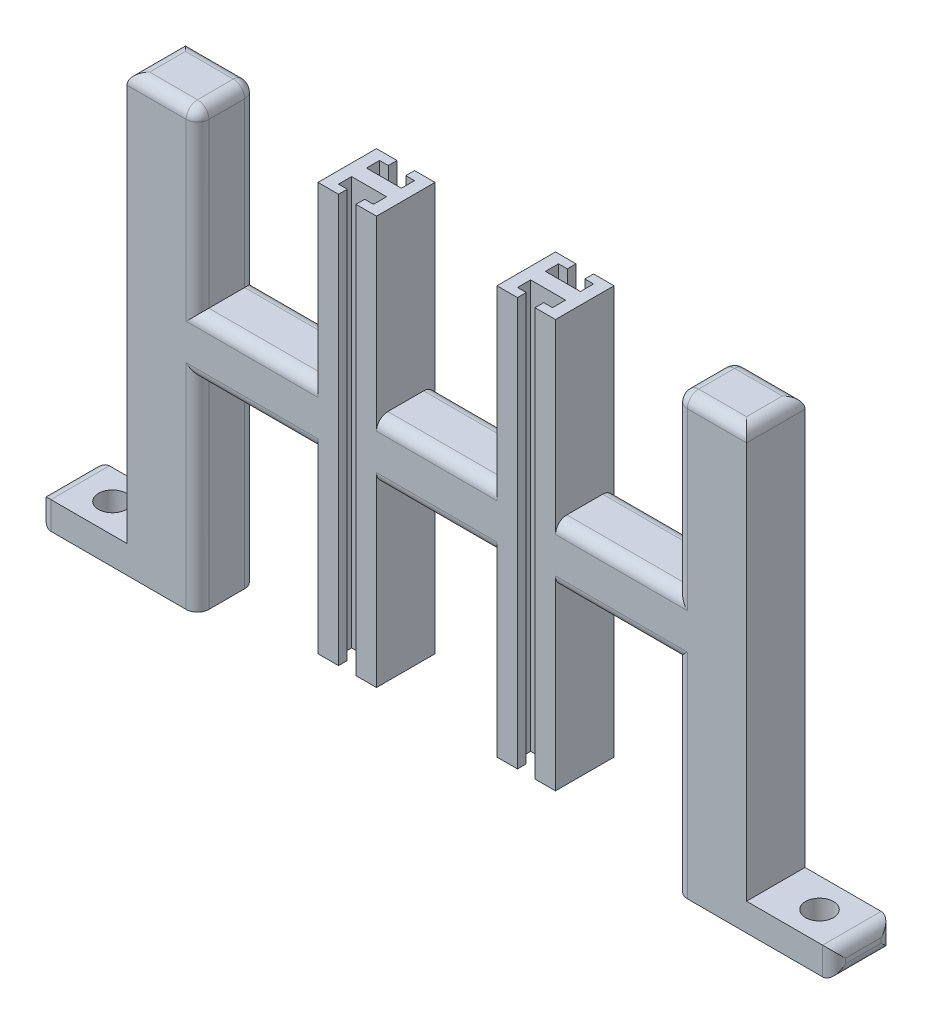
SolidWorks part; units mm, degrees
ref_plane "Front Plane" through (0, 0, 0) normal (0, 0, 1) x (1, 0, 0)
ref_plane "Top Plane" through (0, 0, 0) normal (0, 1, 0) x (1, 0, 0)
ref_plane "Right Plane" through (0, 0, 0) normal (1, 0, 0) x (0, 0, -1)
sketch "Sketch1" plane through (0, 0, 0) normal (0, 0, 1) x (1, 0, 0)
  line L1 (-45, -4.25) -> (45, -4.25)
  line L2 (-45, -4.25) -> (-45, 4.25)
  line L3 (-45, 4.25) -> (45, 4.25)
  line L4 (45, -4.25) -> (45, 4.25)
  line L5 (-45, -4.25) -> (45, 4.25) construction
  line L6 (-45, 4.25) -> (45, -4.25) construction
  point P0 (0, 0)
  dimension "D1" = 8.5
  dimension "D2" = 90
extrude "Boss-Extrude1" add sketch "Sketch1" along normal blind 8.5
sketch "Sketch2" plane through (0, 4.25, 0) normal (0, 1, 0) x (1, 0, 0)
  line L0 (45, -8.5) -> (45, 0) construction
  line L2 (8.75, -8.5) -> (8.75, 0)
  line L4 (0, -13.4309) -> (0, 4.4751) construction
  line L5 (45, 0) -> (-45, 0) construction
  line L6 (-8.75, 0) -> (-17.25, 0)
  line L7 (-17.25, 0) -> (-17.25, -8.5)
  line L8 (45, -8.5) -> (-45, -8.5) construction
  line L9 (-17.25, -8.5) -> (-8.75, -8.5)
  line L10 (-8.75, -8.5) -> (-8.75, 0)
  line L11 (8.75, 0) -> (17.25, 0)
  line L12 (17.25, 0) -> (17.25, -8.5)
  line L13 (17.25, -8.5) -> (8.75, -8.5)
  point P4 (45, -4.25)
  point P16 (-8.75, -4.25)
  point P19 (0, -4.4779)
  dimension "D1" = 17.5
  dimension "D2" = 8.75
  dimension "D3" = 8.5
  dimension "D4" = 8.5
extrude "Boss-Extrude2" add sketch "Sketch2" along normal blind 25.4 and the other way blind 33.9
sketch "Sketch3" plane through (0, 4.25, 0) normal (0, 1, 0) x (1, 0, 0)
  line L0 (-34.75, 0) -> (-34.75, -8.5)
  line L1 (-17.25, 0) -> (-45, 0) construction
  line L3 (-45, -8.5) -> (-45, 0) construction
  line L4 (-17.25, -8.5) -> (-45, -8.5) construction
  line L5 (-45, 0) -> (-34.75, 0)
  line L6 (34.75, 0) -> (34.75, -8.5)
  line L7 (45, 0) -> (17.25, 0) construction
  line L8 (45, -8.5) -> (17.25, -8.5) construction
  line L9 (34.75, -8.5) -> (45, -8.5)
  line L10 (45, 0) -> (45, -8.5)
  line L11 (45, 0) -> (34.75, 0)
  line L12 (-17.25, -8.5) -> (-17.25, 0) construction
  line L13 (17.25, 0) -> (17.25, -8.5) construction
  line L14 (-45, -8.5) -> (-34.75, -8.5)
  line L15 (-45, 0) -> (-45, -8.5)
  dimension "D1" = 17.5
  dimension "D2" = 17.5
extrude "Boss-Extrude3" add sketch "Sketch3" along normal blind 25.4 and the other way blind 37.9
sketch "Sketch4" plane through (45, 0, 0) normal (1, 0, 0) x (0, 0, -1)
  line L0 (-8.5, -33.65) -> (0, -33.65)
  line L1 (0, -33.65) -> (0, -29.65)
  line L2 (0, -33.65) -> (0, 29.65) construction
  line L3 (0, -29.65) -> (-8.5, -29.65)
  line L4 (-8.5, -33.65) -> (-8.5, 29.65) construction
  line L5 (-8.5, -29.65) -> (-8.5, -33.65)
  dimension "D1" = 4
extrude "Boss-Extrude4" add sketch "Sketch4" along normal blind 12.7
sketch "Sketch5" plane through (-45, 0, 0) normal (-1, 0, 0) x (0, 0, 1)
  line L0 (8.5, -33.65) -> (0, -33.65)
  line L1 (0, -33.65) -> (0, -29.65)
  line L2 (0, 29.65) -> (0, -33.65) construction
  line L3 (0, -29.65) -> (8.5, -29.65)
  line L4 (8.5, 29.65) -> (8.5, -33.65) construction
  line L5 (8.5, -29.65) -> (8.5, -33.65)
  point P4 (4.25, -33.65)
  dimension "D1" = 4
extrude "Boss-Extrude5" add sketch "Sketch5" along normal blind 12.7
sketch "Sketch6" plane through (0, -29.65, 0) normal (0, 1, 0) x (1, 0, 0)
  circle A0 centre (51.35, -4.25) radius 2.032
  circle A1 centre (-51.35, -4.25) radius 2.032
extrude "Cut-Extrude1" cut sketch "Sketch6" against normal blind 12.7
sketch "Sketch7" plane through (0, 29.65, 0) normal (0, 1, 0) x (1, 0, 0)
  line L0 (14.27, 0) -> (14.27, -1.27)
  line L1 (14.27, 0) -> (11.73, 0)
  line L2 (17.25, 0) -> (8.75, 0) construction
  line L3 (14.27, -1.27) -> (15.54, -1.27)
  line L4 (15.54, -1.27) -> (15.54, -3.175)
  line L5 (15.54, -3.175) -> (10.46, -3.175)
  line L6 (10.46, -3.175) -> (10.46, -1.27)
  line L7 (10.46, -1.27) -> (11.73, -1.27)
  line L8 (11.73, -1.27) -> (11.73, 0)
  line L10 (0, 14.7364) -> (0, -16.6596) construction
  line L11 (-11.73, -1.27) -> (-11.73, 0)
  line L12 (-10.46, -1.27) -> (-11.73, -1.27)
  line L13 (-10.46, -3.175) -> (-10.46, -1.27)
  line L14 (-15.54, -3.175) -> (-10.46, -3.175)
  line L15 (-15.54, -1.27) -> (-15.54, -3.175)
  line L16 (-14.27, -1.27) -> (-15.54, -1.27)
  line L17 (-14.27, 0) -> (-11.73, 0)
  line L18 (-14.27, 0) -> (-14.27, -1.27)
  line L19 (-17.25, -4.25) -> (18.6184, -4.25) construction
  line L20 (-17.25, 0) -> (-17.25, -8.5) construction
  line L21 (-14.27, -8.5) -> (-14.27, -7.23)
  line L22 (-14.27, -8.5) -> (-11.73, -8.5)
  line L23 (-14.27, -7.23) -> (-15.54, -7.23)
  line L24 (-15.54, -7.23) -> (-15.54, -5.325)
  line L25 (-15.54, -5.325) -> (-10.46, -5.325)
  line L26 (-10.46, -5.325) -> (-10.46, -7.23)
  line L27 (-10.46, -7.23) -> (-11.73, -7.23)
  line L28 (-11.73, -7.23) -> (-11.73, -8.5)
  line L29 (11.73, -7.23) -> (11.73, -8.5)
  line L30 (10.46, -7.23) -> (11.73, -7.23)
  line L31 (10.46, -5.325) -> (10.46, -7.23)
  line L32 (15.54, -5.325) -> (10.46, -5.325)
  line L33 (15.54, -7.23) -> (15.54, -5.325)
  line L34 (14.27, -7.23) -> (15.54, -7.23)
  line L35 (14.27, -8.5) -> (11.73, -8.5)
  line L36 (14.27, -8.5) -> (14.27, -7.23)
  point P4 (13, 0)
  point P11 (13, -3.175)
  dimension "D1" = 1.27
  dimension "D2" = 1.27
  dimension "D3" = 2.54
  dimension "D4" = 1.905
  dimension "D5" = 1.27
  dimension "D6" = 1.27
extrude "Cut-Extrude2" cut sketch "Sketch7" against normal blind 73.406 and the other way blind 9.906
fillet "Fillet2" radius 1.651 36 edges at (57.7, -31.65, 8.5) (57.7, -33.65, 4.25) (57.7, -31.65, 0) (57.7, -29.65, 4.25) (-57.7, -31.65, 8.5) (-57.7, -29.65, 4.25) (-57.7, -31.65, 0) (-57.7, -33.65, 4.25) (26, -4.25, 0) (0, 4.25, 0) (0, 4.25, 8.5) (26, -4.25, 8.5) (0, -4.25, 0) (-26, 4.25, 0) (-26, 4.25, 8.5) (0, -4.25, 8.5) (-26, -4.25, 0) (-26, -4.25, 8.5) (-34.75, 16.95, 8.5) (-34.75, -18.95, 8.5) (-34.75, 16.95, 0) (-34.75, -18.95, 0) (-39.875, 29.65, 0) (-45, 29.65, 4.25) (-39.875, 29.65, 8.5) (-34.75, 29.65, 4.25) (26, 4.25, 0) (26, 4.25, 8.5) (34.75, 16.95, 0) (34.75, -18.95, 0) (34.75, 16.95, 8.5) (34.75, -18.95, 8.5) (39.875, 29.65, 0) (34.75, 29.65, 4.25) (39.875, 29.65, 8.5) (45, 29.65, 4.25)
